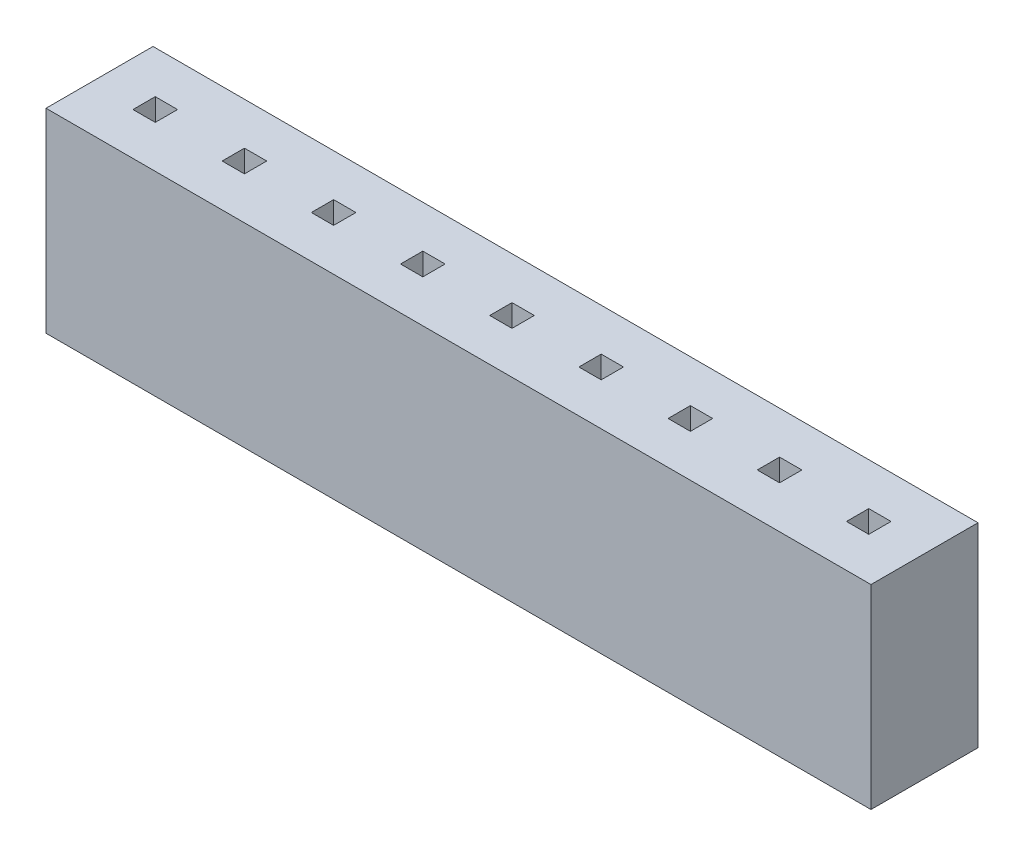
SolidWorks part; units mm, degrees
ref_plane "Front Plane" through (0, 0, 0) normal (0, 0, 1) x (1, 0, 0)
ref_plane "Top Plane" through (0, 0, 0) normal (0, 1, 0) x (1, 0, 0)
ref_plane "Right Plane" through (0, 0, 0) normal (1, 0, 0) x (0, 0, -1)
sketch "Sketch1" plane through (0, 0, 0) normal (0, 1, 0) x (1, 0, 0)
  line L1 (-0.25, -0.2) -> (18.25, -0.2)
  line L2 (-0.25, -0.2) -> (-0.25, 2.2)
  line L3 (-0.25, 2.2) -> (18.25, 2.2)
  line L4 (18.25, -0.2) -> (18.25, 2.2)
extrude "Boss-Extrude1" add sketch "Sketch1" along normal blind 4.37
sketch "Sketch2" plane through (0, 4.37, 0) normal (0, 1, 0) x (1, 0, 0)
  line L0 (2.75, 0.75) -> (3.25, 0.75)
  line L1 (0.75, 0.75) -> (1.25, 0.75)
  line L2 (0.75, 0.75) -> (0.75, 1.25)
  line L3 (0.75, 1.25) -> (1.25, 1.25)
  line L4 (1.25, 0.75) -> (1.25, 1.25)
  line L5 (2.75, 0.75) -> (2.75, 1.25)
  line L6 (2.75, 1.25) -> (3.25, 1.25)
  line L7 (3.25, 0.75) -> (3.25, 1.25)
  line L8 (4.75, 0.75) -> (5.25, 0.75)
  line L9 (4.75, 0.75) -> (4.75, 1.25)
  line L10 (4.75, 1.25) -> (5.25, 1.25)
  line L11 (5.25, 0.75) -> (5.25, 1.25)
  line L12 (6.75, 0.75) -> (7.25, 0.75)
  line L13 (6.75, 0.75) -> (6.75, 1.25)
  line L14 (6.75, 1.25) -> (7.25, 1.25)
  line L15 (7.25, 0.75) -> (7.25, 1.25)
  line L16 (8.75, 0.75) -> (9.25, 0.75)
  line L17 (8.75, 0.75) -> (8.75, 1.25)
  line L18 (8.75, 1.25) -> (9.25, 1.25)
  line L19 (9.25, 0.75) -> (9.25, 1.25)
  line L20 (10.75, 0.75) -> (11.25, 0.75)
  line L21 (10.75, 0.75) -> (10.75, 1.25)
  line L22 (10.75, 1.25) -> (11.25, 1.25)
  line L23 (11.25, 0.75) -> (11.25, 1.25)
  line L24 (12.75, 0.75) -> (13.25, 0.75)
  line L25 (12.75, 0.75) -> (12.75, 1.25)
  line L26 (12.75, 1.25) -> (13.25, 1.25)
  line L27 (13.25, 0.75) -> (13.25, 1.25)
  line L28 (14.75, 0.75) -> (15.25, 0.75)
  line L29 (14.75, 0.75) -> (14.75, 1.25)
  line L30 (14.75, 1.25) -> (15.25, 1.25)
  line L31 (15.25, 0.75) -> (15.25, 1.25)
  line L32 (16.75, 0.75) -> (17.25, 0.75)
  line L33 (16.75, 0.75) -> (16.75, 1.25)
  line L34 (16.75, 1.25) -> (17.25, 1.25)
  line L35 (17.25, 0.75) -> (17.25, 1.25)
  dimension "D1" = 9
extrude "Cut-Extrude1" cut sketch "Sketch2" against normal blind 4.37
